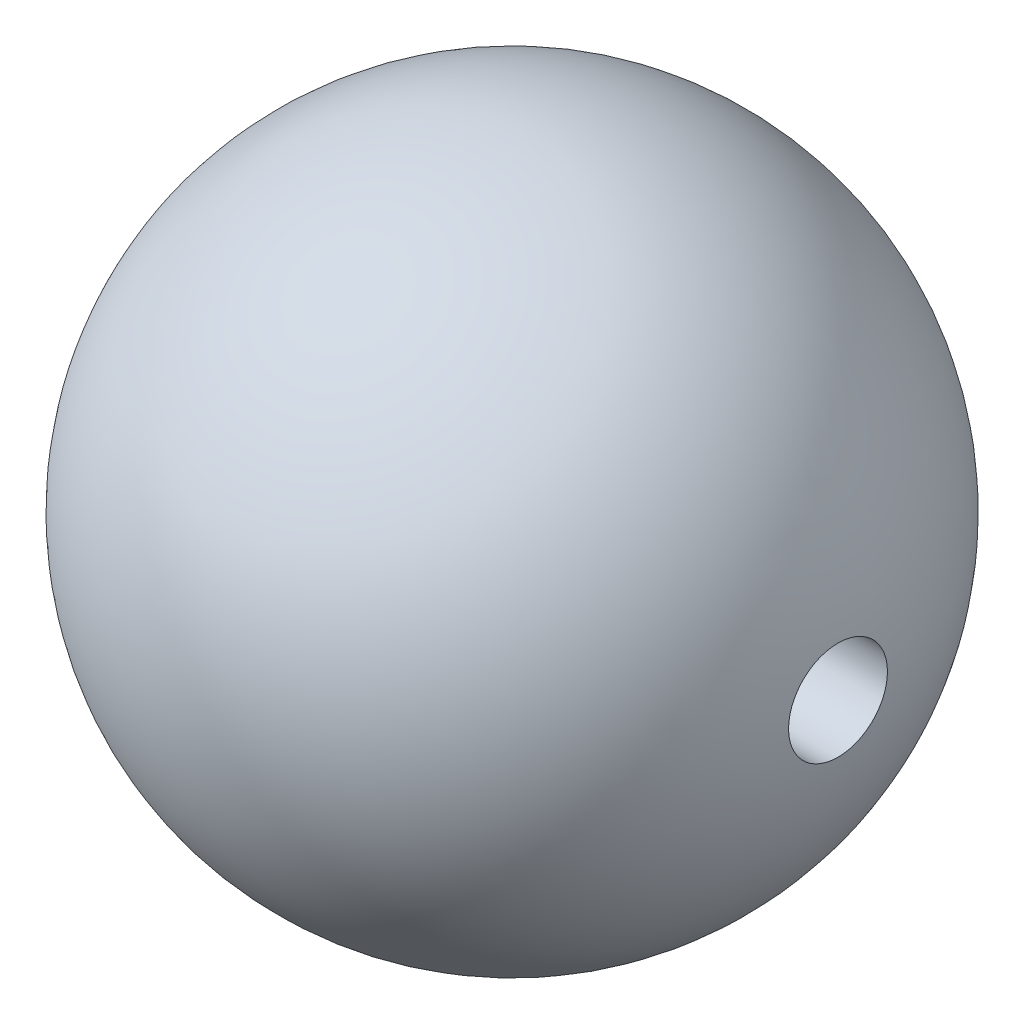
SolidWorks part; units mm, degrees
material "1060 Alloy"
ref_plane "Front Plane" through (0, 0, 0) normal (0, 0, 1) x (1, 0, 0)
ref_plane "Top Plane" through (0, 0, 0) normal (0, 1, 0) x (1, 0, 0)
ref_plane "Right Plane" through (0, 0, 0) normal (1, 0, 0) x (0, 0, -1)
sketch "Sketch1" plane through (0, 0, 0) normal (0, 0, 1) x (1, 0, 0)
  circle A0 centre (0, 0) radius 10
sketch "Sketch2" plane through (0, 0, 0) normal (0, 1, 0) x (1, 0, 0)
  line L1 (0, 0) -> (10, 0)
  line L2 (0, 0) -> (0, 10)
  arc A0 (10, 0) -> (0, 10) centre (0, 0) ccw
revolve "Revolve1" add sketch "Sketch2" angle 360 about L1
mirror "Mirror1" about plane through (0, 0, 0) normal (1, 0, 0) of "Revolve1"
sketch "Sketch3" plane through (0, 0, 0) normal (1, 0, 0) x (0, 0, -1)
  circle A0 centre (0, 0) radius 1.5
sketch "Sketch4" plane through (0, 0, 0) normal (0, 0, 1) x (1, 0, 0)
  line L0 (0, 0) -> (10, 0) construction
  circle A0 centre (0, 0) radius 10 construction
extrude "Cut-Extrude1" cut sketch "Sketch3" along normal up to vertex contours A0
